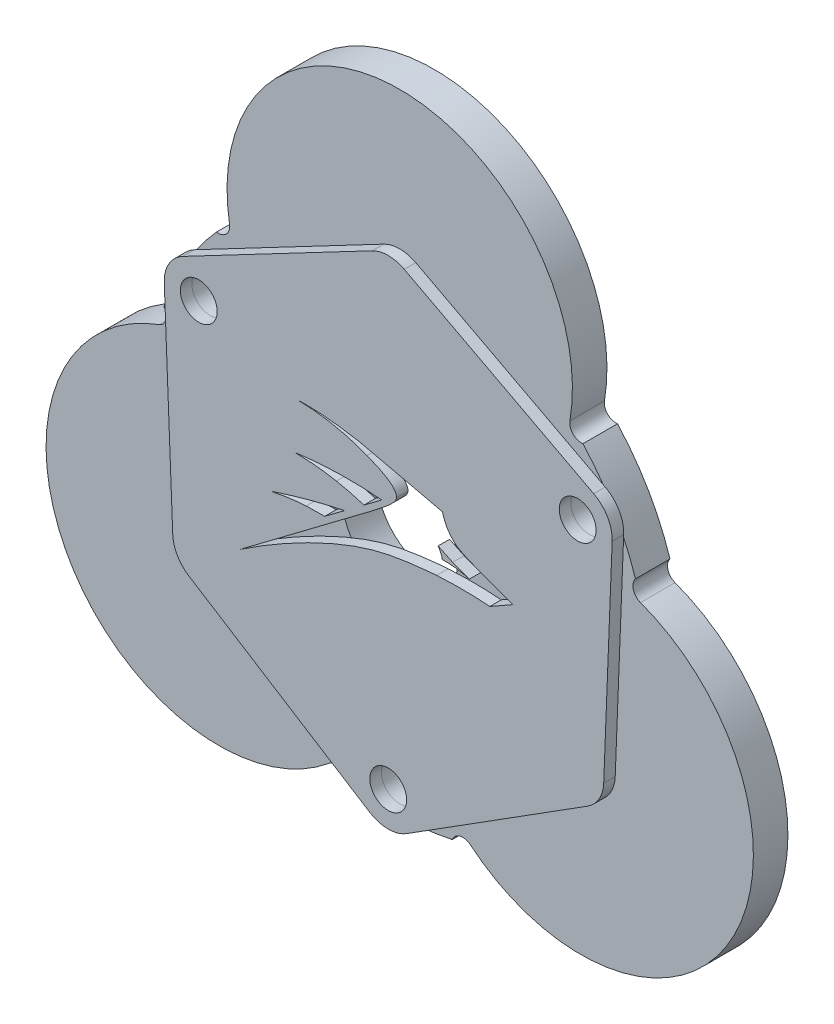
SolidWorks part; units mm, degrees
material "Thornel Mat VMA"
ref_plane "前视基准面" through (0, 0, 0) normal (0, 0, 1) x (1, 0, 0)
ref_plane "上视基准面" through (0, 0, 0) normal (0, 1, 0) x (1, 0, 0)
ref_plane "右视基准面" through (0, 0, 0) normal (1, 0, 0) x (0, 0, -1)
sketch "草图1" plane through (0, 0, 0) normal (0, 0, 1) x (1, 0, 0)
  line L0 (0, 18.15) -> (0, 0) construction
  line L1 (0, 0) -> (16.4545, 9.5) construction
  circle A0 centre (0, 0) radius 18.15 construction
  circle A1 centre (0, 0) radius 5
  circle A2 centre (0, 0) radius 19 construction
  circle A3 centre (0, 18.15) radius 2
  circle A4 centre (16.4545, 9.5) radius 1.6
  circle A5 centre (15.7184, -9.075) radius 2
  circle A6 centre (0, -19) radius 1.6
  circle A7 centre (-15.7184, -9.075) radius 2
  circle A8 centre (-16.4545, 9.5) radius 1.6
  circle A9 centre (0, 0) radius 21.5
  point P19 (0, 0)
  dimension "D1" = 36.3
  dimension "D2" = 38
  dimension "D3" = 10
  dimension "D4" = 4
  dimension "D6" = 3.2
  dimension "D8" = 43
  dimension "D5" = 60
  dimension "D7" = 3
extrude "凸台-拉伸1" add sketch "草图1" along normal blind 3
sketch "草图2" plane through (0, 0, 3) normal (0, 0, 1) x (1, 0, 0)
  arc A0 (14.4322, 14.0618) -> (-14.4322, 14.0618) centre (0, 18.15) ccw
  arc A1 (14.4322, 14.0618) -> (-14.4322, 14.0618) centre (0, 0) ccw
  circle A2 centre (0, 18.15) radius 2 construction
  dimension "D1" = 30
extrude "凸台-拉伸2" add sketch "草图2" against normal up to surface (3 mm away) up to face at (21.5, 0, 0)
sketch "草图3" plane through (0, 0, 3) normal (0, 0, 1) x (1, 0, 0)
  circle A0 centre (-15.7691, 15.4415) radius 1
  arc A1 (14.7835, 15.6108) -> (-14.7835, 15.6108) centre (0, 18.15) ccw construction
  circle A2 centre (15.7691, 15.4415) radius 1
  dimension "D1" = 2
extrude "切除-拉伸1" cut sketch "草图3" against normal through all
pattern_circular "阵列(圆周)1" count 3 over 360 about axis through (0, 0, 0) along (0, 0, 1) of "凸台-拉伸2", "切除-拉伸1"
sketch "草图6" plane through (0, 0, 3) normal (0, 0, 1) x (1, 0, 0)
  line L9 (-17.8504, 12.1554) -> (-1.3959, 20.8054)
  line L10 (1.3959, 20.8054) -> (17.8504, 12.1554)
  line L11 (19.4521, 9.3812) -> (18.716, -9.1938)
  line L12 (17.3201, -11.6116) -> (1.6017, -21.5366)
  line L13 (-1.6017, -21.5366) -> (-17.3201, -11.6116)
  line L14 (-18.716, -9.1938) -> (-19.4521, 9.3812)
  circle A28 centre (16.4545, 9.5) radius 1.6 construction
  circle A29 centre (0, -19) radius 1.6 construction
  circle A30 centre (-16.4545, 9.5) radius 1.6 construction
  circle A31 centre (16.4545, 9.5) radius 1.6
  circle A32 centre (0, -19) radius 1.6
  circle A33 centre (-16.4545, 9.5) radius 1.6
  arc A34 (1.6017, -21.5366) -> (-1.6017, -21.5366) centre (0, -19) cw
  arc A35 (-17.3201, -11.6116) -> (-18.716, -9.1938) centre (-15.7184, -9.075) cw
  arc A36 (17.8504, 12.1554) -> (19.4521, 9.3812) centre (16.4545, 9.5) cw
  arc A37 (18.716, -9.1938) -> (17.3201, -11.6116) centre (15.7184, -9.075) cw
  arc A38 (-1.3959, 20.8054) -> (1.3959, 20.8054) centre (0, 18.15) cw
  arc A39 (-17.8504, 12.1554) -> (-19.4521, 9.3812) centre (-16.4545, 9.5) ccw
  circle A40 centre (0, 18.15) radius 2 construction
  circle A41 centre (15.7184, -9.075) radius 2 construction
  circle A42 centre (-15.7184, -9.075) radius 2 construction
  dimension "D1" = 3
extrude "凸台-拉伸3" add sketch "草图6" along normal blind 1 separate body
sketch "草图7" plane through (0, 0, 4) normal (0, 0, 1) x (1, 0, 0)
  line L0 (-0.5672, 2.4763) -> (-2.1081, 1.3206)
  line L1 (-3.797, 0.061) -> (-5.5159, -1.2283)
  spline S0 degree 3 poles (10.8348, 0.305) (9.8961, 0.6306) (8.8431, 1.012) (7.6961, 1.4545) knots 15 15 15 15 16 16 16 16
  spline S1 degree 3 poles (8.8222, -0.8405) (9.4931, -0.4587) (10.164, -0.0769) (10.8348, 0.305) knots 14 14 14 14 15 15 15 15
  spline S2 degree 3 poles (4.2082, -0.8101) (6.0034, -0.6951) (7.5688, -0.7436) (8.8222, -0.8405) knots 13 13 13 13 14 14 14 14
  spline S3 degree 3 poles (-12.8344, -7.3694) (-12.2884, -6.9952) (-5.6049, -2.4704) (-0.0085, -1.3567) (2.0412, -0.9488) (4.2082, -0.8101) (4.2082, -0.8101) knots 11 11 11 11 12 12 12 13 13 13 13
  spline S4 degree 3 poles (-2.8305, 0.1613) (-2.8517, 0.1455) (-4.5485, -1.1272) (-4.5495, -1.1279) (-5.3514, -1.7294) (-7.4362, -3.2985) (-12.8344, -7.3694) knots 9 9 9 9 10 10 10 11 11 11 11
  spline S5 degree 3 poles (-1.4541, 1.1937) (-1.7887, 0.9337) (-1.9598, 0.8144) (-2.8305, 0.1613) knots 8 8 8 8 9 9 9 9
  spline S6 degree 3 poles (0.7203, 3.3025) (0.7171, 2.8806) (-0.0066, 2.3183) (-1.4541, 1.1937) knots 7 7 7 7 8 8 8 8
  spline S7 degree 3 poles (-1.8306, 5.1766) (-0.8438, 4.7836) (0.7266, 4.1408) (0.7203, 3.3025) knots 6 6 6 6 7 7 7 7
  spline S8 degree 3 poles (-7.7912, 6.3479) (-7.7922, 6.3306) (-4.9894, 6.435) (-1.8306, 5.1766) knots 5 5 5 5 6 6 6 6
  spline S9 degree 3 poles (-2.5204, 5.8924) (-5.6303, 6.4764) (-7.7904, 6.3632) (-7.7912, 6.3479) knots 4 4 4 4 5 5 5 5
  spline S10 degree 3 poles (0.9415, 5.0986) (-1.5311, 5.6802) (-1.8179, 5.7606) (-2.5204, 5.8924) knots 3 3 3 3 4 4 4 4
  spline S11 degree 3 poles (4.7172, 4.2203) (3.8463, 4.4206) (2.5381, 4.723) (0.9415, 5.0986) knots 2 2 2 2 3 3 3 3
  spline S12 degree 3 poles (5.4381, 2.7624) (5.0047, 3.279) (4.8116, 3.834) (4.7172, 4.2203) knots 1 1 1 1 2 2 2 2
  spline S13 degree 3 poles (7.6961, 1.4545) (6.5392, 1.9008) (5.9485, 2.154) (5.4381, 2.7624) knots 0 0 0 0 1 1 1 1
  spline S14 degree 3 poles (5.8972, 0.5664) (5.4452, 0.6255) (5.0383, 0.637) (4.6929, 0.6266) knots 5 5 5 5 6 6 6 6
  spline S15 degree 3 poles (7.0419, 0.3254) (6.7186, 0.4201) (6.3342, 0.5093) (5.8972, 0.5664) knots 4 4 4 4 5 5 5 5
  spline S16 degree 3 poles (5.5961, 0.8675) (6.1049, 0.6502) (6.5899, 0.4721) (7.0419, 0.3254) knots 3 3 3 3 4 4 4 4
  spline S17 degree 3 poles (4.3316, 1.4696) (4.7159, 1.267) (5.1376, 1.0633) (5.5961, 0.8675) knots 2 2 2 2 3 3 3 3
  spline S18 degree 3 poles (4.5725, 1.0481) (4.4979, 1.2282) (4.4076, 1.3687) (4.3316, 1.4696) knots 1 1 1 1 2 2 2 2
  spline S19 degree 3 poles (4.6929, 0.6266) (4.6738, 0.7423) (4.6388, 0.8881) (4.5725, 1.0481) knots 0 0 0 0 1 1 1 1
  spline S20 degree 3 poles (-2.1081, 1.3206) (-2.8141, 1.5493) (-3.6136, 1.7644) (-4.4986, 1.9328) knots 1 1 1 1 2 2 2 2
  spline S21 degree 3 poles (-4.4986, 1.9328) (-5.8399, 2.188) (-7.0541, 2.2745) (-8.0823, 2.2801) knots 2 2 2 2 3 3 3 3
  spline S22 degree 3 poles (-8.0823, 2.2801) (-6.9355, 2.4426) (-5.6424, 2.564) (-4.2253, 2.5965) knots 3 3 3 3 4 4 4 4
  spline S23 degree 3 poles (-4.2253, 2.5965) (-2.8915, 2.6271) (-1.6652, 2.5738) (-0.5672, 2.4763) knots 4 4 4 4 5 5 5 5
  spline S24 degree 3 poles (-5.5159, -1.2283) (-6.0228, -1.2178) (-6.5612, -1.2257) (-7.1275, -1.2591) knots 1 1 1 1 2 2 2 2
  spline S25 degree 3 poles (-7.1275, -1.2591) (-8.2539, -1.3254) (-9.2724, -1.4796) (-10.1648, -1.6693) knots 2 2 2 2 3 3 3 3
  spline S26 degree 3 poles (-10.1648, -1.6693) (-9.218, -1.3488) (-8.2113, -1.0372) (-7.147, -0.745) knots 3 3 3 3 4 4 4 4
  spline S27 degree 3 poles (-7.147, -0.745) (-5.9802, -0.4246) (-4.8605, -0.1592) (-3.797, 0.061) knots 4 4 4 4 5 5 5 5
extrude "切除-拉伸2" cut sketch "草图7" against normal through all
move or copy body "实体-移动/复制1" [suppressed]
